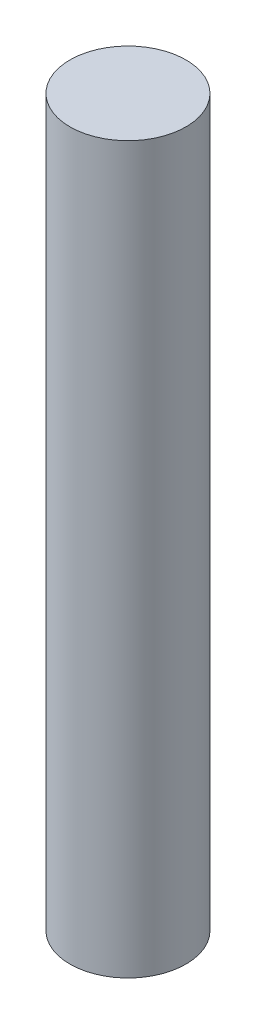
SolidWorks part; units mm, degrees
ref_plane "Front" through (0, 0, 0) normal (0, 0, 1) x (1, 0, 0)
ref_plane "Top" through (0, 0, 0) normal (0, 1, 0) x (1, 0, 0)
ref_plane "Right" through (0, 0, 0) normal (1, 0, 0) x (0, 0, -1)
sketch "Sketch1" plane through (0, 0, 0) normal (0, 1, 0) x (1, 0, 0)
  circle A0 centre (0, 0) radius 4
  dimension "D1" = 8
extrude "Boss-Extrude1" add sketch "Sketch1" along normal blind 50
